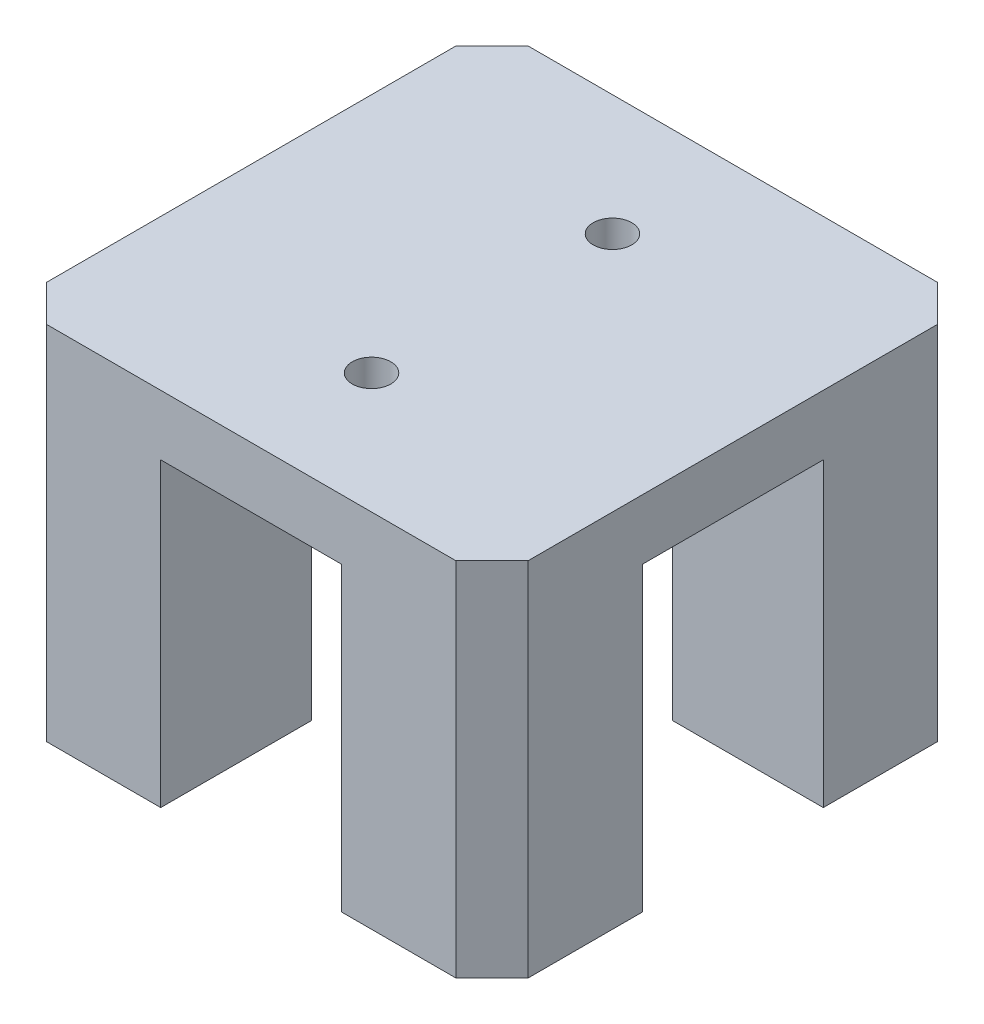
SolidWorks part; units mm, degrees
ref_plane "Ebene vorne" through (0, 0, 0) normal (0, 0, 1) x (1, 0, 0)
ref_plane "Ebene oben" through (0, 0, 0) normal (0, 1, 0) x (1, 0, 0)
ref_plane "Ebene rechts" through (0, 0, 0) normal (1, 0, 0) x (0, 0, -1)
sketch "Skizze1" plane through (0, 0, 0) normal (0, 1, 0) x (1, 0, 0)
  line L1 (-20, 20) -> (20, 20)
  line L2 (-20, 20) -> (-20, -20)
  line L3 (-20, -20) -> (20, -20)
  line L4 (20, 20) -> (20, -20)
  point P4 (0, 20)
  point P6 (20, 0)
  dimension "D1" = 40
  dimension "D2" = 40
extrude "Aufsatz-Linear austragen1" add sketch "Skizze1" along normal blind 30
chamfer "Fase1" distance 3 angle 45 4 edges at (-20, 15, -20) (20, 15, -20) (20, 15, 20) (-20, 15, 20)
sketch "Skizze2" plane through (0, 0, 0) normal (0, -1, 0) x (1, 0, 0)
  line L0 (-20, -17) -> (-20, 17) construction
  line L1 (-20, 7.5) -> (-7.5, 7.5)
  line L2 (-20, 7.5) -> (-20, -7.5)
  line L3 (-20, -7.5) -> (-7.5, -7.5)
  line L4 (20, 7.5) -> (20, -7.5)
  line L5 (20, 17) -> (20, -17) construction
  line L6 (-17, 20) -> (17, 20) construction
  line L7 (-7.5, 20) -> (7.5, 20)
  line L8 (-7.5, 20) -> (-7.5, 7.5)
  line L9 (-7.5, -20) -> (7.5, -20)
  line L10 (7.5, 20) -> (7.5, 7.5)
  line L11 (17, -20) -> (-17, -20) construction
  line L12 (7.5, 7.5) -> (20, 7.5)
  line L13 (-7.5, -7.5) -> (-7.5, -20)
  line L14 (7.5, -7.5) -> (20, -7.5)
  line L15 (7.5, -7.5) -> (7.5, -20)
  point P16 (0, 20)
  point P18 (-20, 0)
extrude "Schnitt-Linear austragen1" cut sketch "Skizze2" against normal offset from surface (25 mm away) 5 up to face at (0, 30, 0)
hole_wizard "Durchgangsloch für M31" positions "Skizze4" profile "Skizze5" hole size "M3" standard "DIN" end condition through all
sketch "Skizze4" plane through (0, 30, 0) normal (0, 1, 0) x (1, 0, 0)
  line L0 (17, 20) -> (-17, 20) construction
  line L1 (-17, -20) -> (17, -20) construction
  point P0 (0, 10)
  point P2 (0, -10)
  dimension "D1" = 10
  dimension "D2" = 10
sketch "Skizze5" plane through (0, 30, -10) normal (1, 0, 0) x (0, 0, 1)
  line L0 (0, 0) -> (0, 30)
  line L1 (0, 30) -> (1.6, 30)
  line L2 (1.6, 30) -> (1.6, 0)
  line L5 (1.6, 0) -> (0, 0)
  line L11 (0, -6.35) -> (0, 107.95) construction
  dimension "Bohrerdurchmesser" = 3.2
  dimension "Bohrungstiefe" = 30
